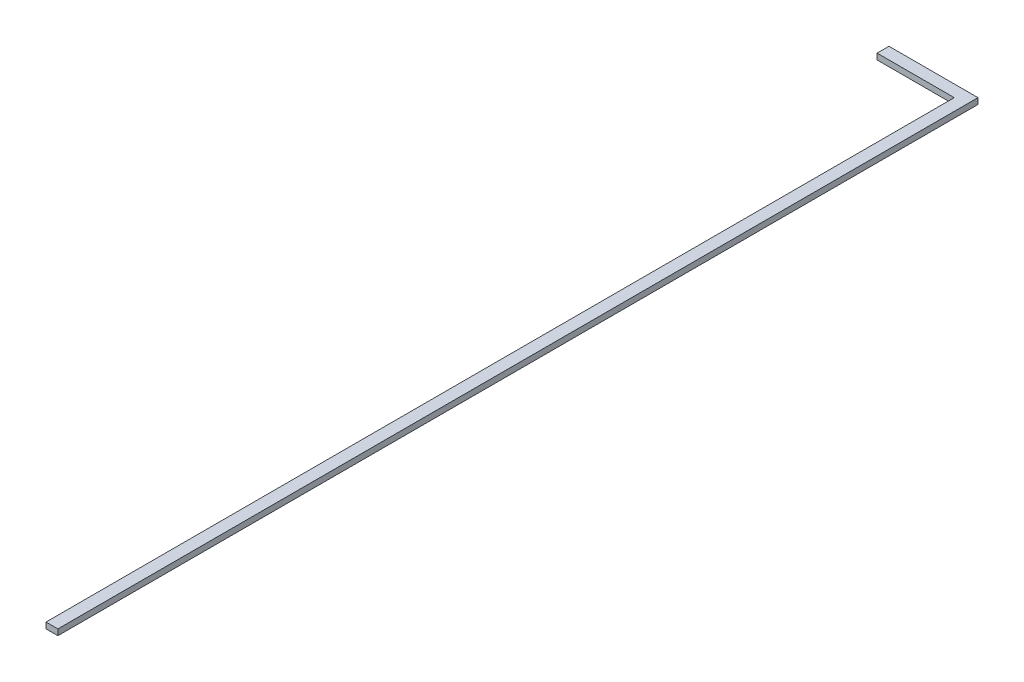
SolidWorks part; units mm, degrees
ref_plane "Face" through (0, 0, 0) normal (0, 0, 1) x (1, 0, 0)
ref_plane "Dessus" through (0, 0, 0) normal (0, 1, 0) x (1, 0, 0)
ref_plane "Droite" through (0, 0, 0) normal (1, 0, 0) x (0, 0, -1)
sketch "Esquisse1" plane through (0, 0, 0) normal (0, 1, 0) x (1, 0, 0)
  line L0 (0, 0) -> (0, 20)
  line L1 (0, 20) -> (150, 20)
  line L2 (150, 20) -> (150, -1530)
  line L3 (0, 0) -> (130, 0)
  line L4 (130, 0) -> (130, -1530)
  line L5 (130, -1530) -> (150, -1530)
  dimension "D1" = 20
  dimension "D2" = 20
  dimension "D3" = 1550
  dimension "D4" = 150
extrude "Extrusion1" add sketch "Esquisse1" along normal blind 10
